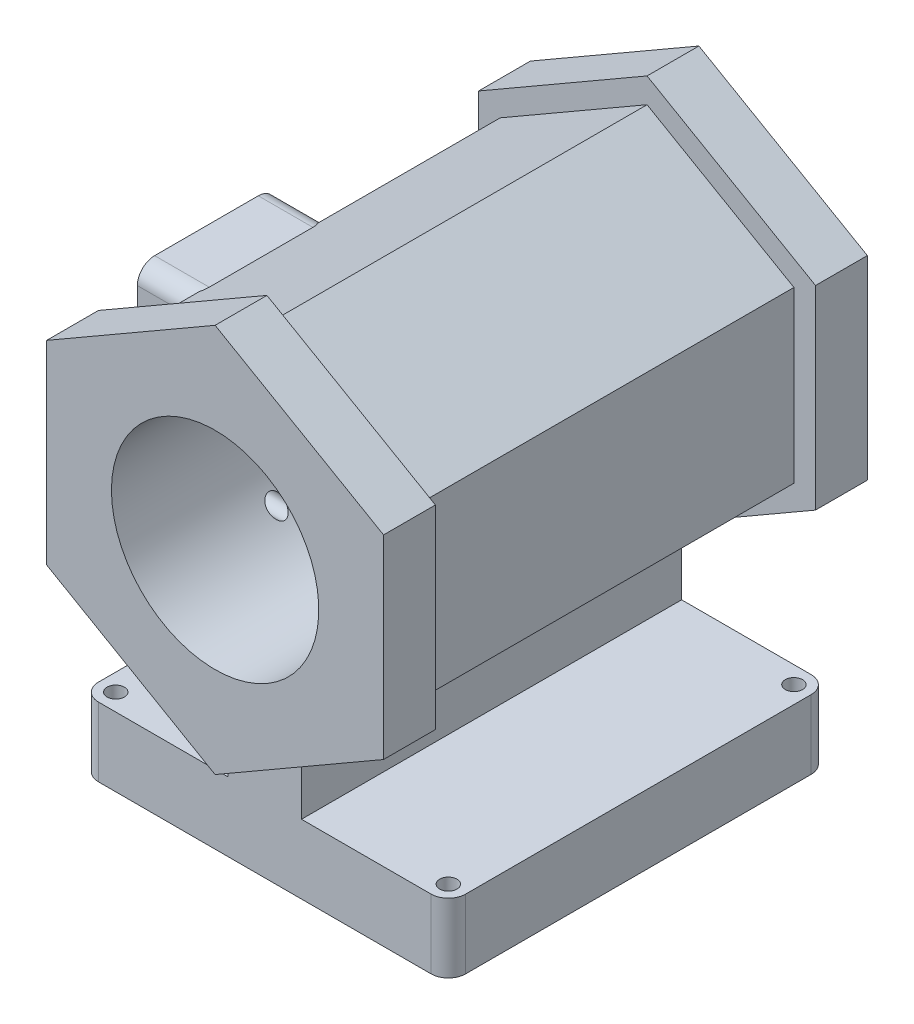
SolidWorks part; units mm, degrees
ref_plane "Front Plane" through (0, 0, 0) normal (0, 0, 1) x (1, 0, 0)
ref_plane "Top Plane" through (0, 0, 0) normal (0, 1, 0) x (1, 0, 0)
ref_plane "Right Plane" through (0, 0, 0) normal (1, 0, 0) x (0, 0, -1)
sketch "Sketch1" plane through (0, 0, 0) normal (0, 0, 1) x (1, 0, 0)
  line L0 (2667, -4572) -> (2667, -3556)
  line L1 (0, 2492.9985) -> (-2159, 1246.4992)
  line L2 (-2159, 1246.4992) -> (-2159, -1246.4992)
  line L3 (-2159, -1246.4992) -> (-571.7504, -2162.8982)
  line L4 (508, -2199.7045) -> (2159, -1246.4992)
  line L5 (2159, -1246.4992) -> (2159, 1246.4992)
  line L6 (2159, 1246.4992) -> (0, 2492.9985)
  line L7 (0, -4572) -> (2667, -4572)
  line L8 (0, -4572) -> (-2730.7504, -4572)
  line L9 (-2730.7504, -4572) -> (-2730.7504, -3556)
  line L10 (-2730.7504, -3556) -> (-571.7504, -3556)
  line L11 (2667, -3556) -> (508, -3556)
  line L12 (-571.7504, -3556) -> (-571.7504, -2162.8982)
  line L13 (508, -3556) -> (508, -2199.7045)
  circle A0 centre (0, 0) radius 2159 construction
  dimension "D1" = 4318
extrude "Boss-Extrude1" add sketch "Sketch1" along normal blind 5588
sketch "Sketch3" plane through (0, 0, 5588) normal (0, 0, 1) x (1, 0, 0)
  line L1 (0, 2859.6159) -> (-2476.5, 1429.8079)
  line L2 (-2476.5, 1429.8079) -> (-2476.5, -1429.8079)
  line L3 (-2476.5, -1429.8079) -> (0, -2859.6159)
  line L4 (0, -2859.6159) -> (2476.5, -1429.8079)
  line L5 (2476.5, -1429.8079) -> (2476.5, 1429.8079)
  line L6 (2476.5, 1429.8079) -> (0, 2859.6159)
  circle A0 centre (0, 0) radius 2476.5 construction
  dimension "D1" = 4953
extrude "Boss-Extrude2" add sketch "Sketch3" along normal blind 762
sketch "Sketch4" plane through (0, 0, 0) normal (0, 0, -1) x (-1, 0, 0)
  line L1 (0, 2859.6159) -> (-2476.5, 1429.8079)
  line L2 (-2476.5, 1429.8079) -> (-2476.5, -1429.8079)
  line L3 (-2476.5, -1429.8079) -> (0, -2859.6159)
  line L4 (0, -2859.6159) -> (2476.5, -1429.8079)
  line L5 (2476.5, -1429.8079) -> (2476.5, 1429.8079)
  line L6 (2476.5, 1429.8079) -> (0, 2859.6159)
  circle A0 centre (0, 0) radius 2476.5 construction
extrude "Boss-Extrude3" add sketch "Sketch4" along normal blind 762
sketch "Sketch5" plane through (-2159, 0, 0) normal (-1, 0, 0) x (0, 0, 1)
  line L2 (6350, 1429.8079) -> (6350, -1429.8079) construction
  line L3 (2540, -1270) -> (4572, -1270)
  line L4 (2540, -1270) -> (2540, 1270)
  line L5 (2540, 1270) -> (4572, 1270)
  line L6 (4572, -1270) -> (4572, 1270)
  line L7 (2540, -1270) -> (4572, 1270) construction
  line L8 (2540, 1270) -> (4572, -1270) construction
  point P5 (3556, 0)
  point P10 (6350, 0)
  dimension "D1" = 2794
  dimension "D2" = 2032
  dimension "D3" = 2540
extrude "Boss-Extrude4" add sketch "Sketch5" along normal blind 762 and the other way blind 762
fillet "Fillet8" radius 254 8 edges at (2667, -4064, 5588) (2667, -4064, 0) (-2730.7504, -4064, 0) (-2730.7504, -4064, 5588) (-2519.6477, 1270, 4572) (-2519.6477, 1270, 2540) (-2519.6477, -1270, 4572) (-2519.6477, -1270, 2540)
sketch "Sketch6" plane through (-2921, 0, 0) normal (-1, 0, 0) x (0, 0, 1)
  circle A0 centre (3556, 0) radius 762
  dimension "D1" = 1524
extrude "Cut-Extrude1" cut sketch "Sketch6" against normal blind 3035.554
sketch "Sketch7" plane through (0, 0, -762) normal (0, 0, -1) x (-1, 0, 0)
  circle A0 centre (0, 0) radius 1524
  dimension "D1" = 3048
extrude "Cut-Extrude2" cut sketch "Sketch7" against normal through all
sketch "Sketch10" plane through (-2921, 0, 0) normal (-1, 0, 0) x (0, 0, 1)
  circle A0 centre (4318, -1016) radius 127
  circle A1 centre (4318, 1016) radius 127
  circle A2 centre (2794, 1016) radius 127
  circle A3 centre (2794, -1016) radius 127
extrude "Cut-Extrude3" cut sketch "Sketch10" against normal blind 2538.476
sketch "Sketch11" plane through (0, -4572, 0) normal (0, -1, 0) x (1, 0, 0)
  circle A0 centre (-2476.7504, 254) radius 127
  circle A1 centre (2413, 254) radius 127
  circle A2 centre (2413, 5334) radius 127
  circle A3 centre (-2476.7504, 5334) radius 127
sketch "Sketch12" plane through (0, -4572, 0) normal (0, -1, 0) x (1, 0, 0)
extrude "Cut-Extrude4" cut sketch "Sketch11" against normal blind 1783.588
